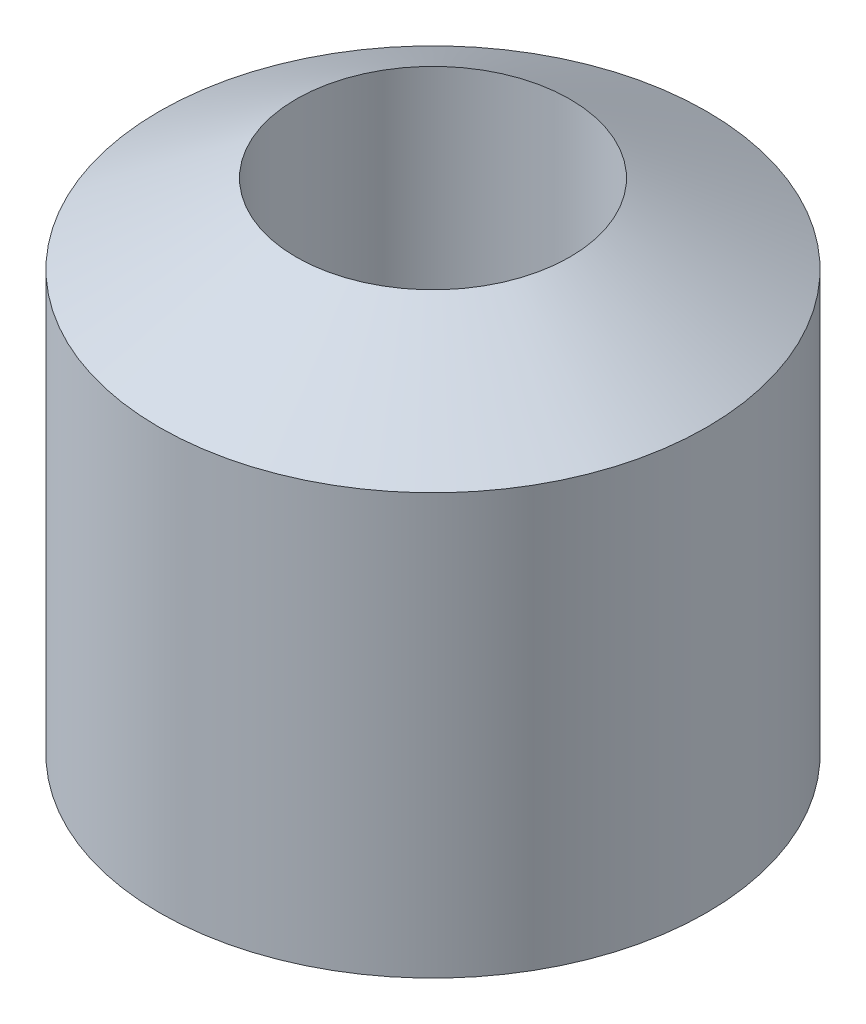
SolidWorks part; units mm, degrees
ref_plane "Front Plane" through (0, 0, 0) normal (0, 0, 1) x (1, 0, 0)
ref_plane "Top Plane" through (0, 0, 0) normal (0, 1, 0) x (1, 0, 0)
ref_plane "Right Plane" through (0, 0, 0) normal (1, 0, 0) x (0, 0, -1)
sketch "Sketch1" plane through (0, 0, 0) normal (0, 0, 1) x (1, 0, 0)
  line L0 (0, 91.25) -> (0, -80.25) construction
  line L1 (14, 29.5829) -> (14, -29.5829)
  line L2 (14, -29.5829) -> (28, -21.5)
  line L3 (28, -21.5) -> (28, 21.5)
  line L4 (28, 21.5) -> (14, 29.5829)
  point P5 (14, 0)
  point P8 (28, 0)
  dimension "D1" = 43
  dimension "D2" = 56
  dimension "D3" = 60
  dimension "D4" = 14
revolve "Revolve1" add sketch "Sketch1" angle 360 about L0
